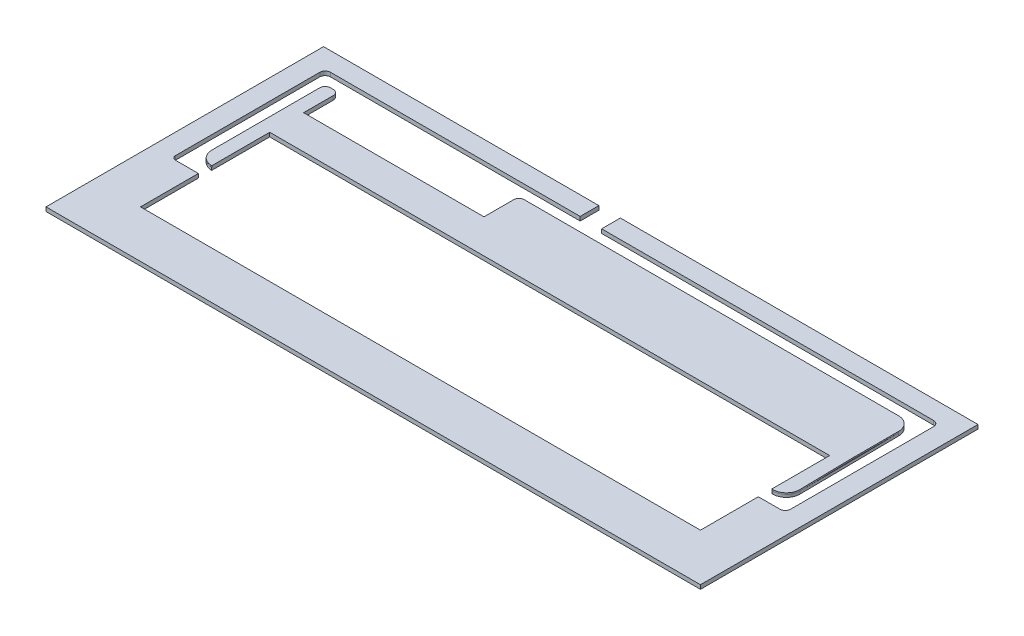
SolidWorks part; units mm, degrees
other "Marca1"
sketch "Croquis6" plane through (483.1, 12, 3.1) normal (0.4175, 0.3737, 0.8283) x (0.8528, 0.1536, -0.4991)
material "Balsa"
ref_plane "Alzado" through (0, 0, 0) normal (0, 0, 1) x (1, 0, 0)
ref_plane "Planta" through (0, 0, 0) normal (0, 1, 0) x (1, 0, 0)
ref_plane "Vista lateral" through (0, 0, 0) normal (1, 0, 0) x (0, 0, -1)
sketch "Croquis1" plane through (0, 0, 0) normal (0, 1, 0) x (1, 0, 0)
  line L0 (0, 0) -> (-3.1, 0) construction
  line L1 (0, 0) -> (480, 0)
  line L2 (0, 0) -> (0, 200)
  line L3 (0, 200) -> (480, 200)
  line L4 (480, 0) -> (480, 200)
  line L5 (0, 0) -> (0, -3.1) construction
  line L6 (-3.1, 0) -> (-3.1, -3.1) construction
  line L7 (-3.1, -3.1) -> (0, -3.1) construction
  line L8 (480, 200) -> (480, 203.1) construction
  line L9 (480, 203.1) -> (483.1, 203.1) construction
  line L11 (-3.1, -3.1) -> (483.1, -3.1)
  line L12 (-3.1, -3.1) -> (-3.1, 203.1)
  line L13 (-3.1, 203.1) -> (483.1, 203.1)
  line L14 (483.1, -3.1) -> (483.1, 203.1)
extrude "Saliente-Extruir1" add sketch "Croquis1" along normal blind 12 contours L1 L4 L3 L2 | L11 L14 L13 L12 L4 L1 L2 L3
sketch "Croquis2" plane through (0, 12, 0) normal (0, 1, 0) x (1, 0, 0)
  line L0 (21.9636, 184.1902) -> (21.9636, 179.1902) construction
  line L1 (17, 184.1902) -> (17, 189.1902) construction
  line L2 (17, 189.1902) -> (16, 189.1902)
  line L3 (28, 184.1902) -> (58, 184.1902) construction
  line L4 (32, 128) -> (448, 128)
  line L6 (32, 32) -> (448, 32)
  line L8 (32, 128) -> (448, 32) construction
  line L9 (32, 32) -> (448, 128) construction
  line L10 (32, 80) -> (17, 80) construction
  line L15 (17, 184.1902) -> (12, 184.1902) construction
  line L16 (28, 184.1902) -> (17, 184.1902) construction
  line L17 (17, 184.1902) -> (17, 80) construction
  line L18 (17, 184.1902) -> (17, 149.1902) construction
  line L19 (12, 185.1902) -> (12, 184.1902)
  line L20 (12, 146.1902) -> (12, 184.1902)
  line L21 (463, 189.1902) -> (464, 189.1902)
  line L22 (17, 80) -> (12, 80) construction
  line L23 (17, 80) -> (17, 75) construction
  line L24 (12, 184.1902) -> (12, 80)
  line L25 (12, 80) -> (12, 78)
  line L26 (15, 75) -> (17, 75)
  line L27 (17, 75) -> (32, 75)
  line L28 (17, 80) -> (21.9636, 80) construction
  line L29 (468, 185.1902) -> (468, 79)
  line L30 (31.9636, 85) -> (32, 85)
  line L31 (463, 189.1902) -> (448, 189.1902)
  line L32 (21.9636, 95) -> (21.9636, 175.1902)
  line L33 (25.9636, 179.1902) -> (28, 179.1902)
  line L34 (58, 184.1902) -> (448, 184.1902) construction
  line L35 (448, 80) -> (463, 80) construction
  line L36 (463, 80) -> (463, 184.1902) construction
  line L37 (463, 184.1902) -> (448, 184.1902) construction
  line L38 (459, 75) -> (459, 85) construction
  line L39 (448.8054, 85) -> (448, 85)
  line L40 (459, 75) -> (448, 75)
  line L41 (458.8036, 95.1927) -> (458.0364, 135)
  line L42 (32, 179.1902) -> (32, 189.1902) construction
  line L43 (448.0364, 125) -> (448, 125)
  line L44 (32, 189.1902) -> (17, 189.1902)
  line L45 (458.0364, 135) -> (458.0364, 169.1902)
  line L46 (464, 75) -> (459, 75)
  line L47 (166, 189.1902) -> (448, 189.1902)
  line L48 (32, 189.1902) -> (166, 189.1902)
  line L50 (32, 153.1902) -> (166, 153.1902)
  line L52 (448.0364, 179.1902) -> (170, 179.1902)
  line L53 (166, 175.1902) -> (166, 153.1902)
  line L54 (32, 175.1902) -> (32, 153.1902)
  line L55 (32, 128) -> (32, 85)
  line L56 (32, 75) -> (32, 32)
  line L57 (32, 85) -> (32, 75)
  line L58 (448, 128) -> (448, 85)
  line L59 (448, 32) -> (448, 75)
  line L60 (448, 85) -> (448, 75)
  line L61 (201.4487, 189.1902) -> (201.4487, 203.1)
  line L62 (-3.1, 203.1) -> (483.1, 203.1) construction
  line L63 (201.4487, 203.1) -> (217.4247, 203.1)
  line L64 (217.4247, 203.1) -> (217.4247, 189.1902)
  arc A0 (458.8036, 95.1927) -> (448.8054, 85) centre (448.8054, 95) cw
  arc A1 (458.0364, 169.1902) -> (448.0364, 179.1902) centre (448.0364, 169.1902) ccw
  arc A2 (21.9636, 95) -> (31.9636, 85) centre (31.9636, 95) ccw
  arc A3 (16, 189.1902) -> (12, 185.1902) centre (16, 185.1902) ccw
  arc A4 (464, 189.1902) -> (468, 185.1902) centre (464, 185.1902) cw
  arc A5 (468, 79) -> (464, 75) centre (464, 79) cw
  arc A6 (170, 179.1902) -> (166, 175.1902) centre (170, 175.1902) ccw
  arc A7 (12, 78) -> (15, 75) centre (15, 78) ccw
  arc A8 (21.9636, 175.1902) -> (25.9636, 179.1902) centre (25.9636, 175.1902) cw
  arc A9 (28, 179.1902) -> (32, 175.1902) centre (28, 175.1902) cw
  point P6 (240, 80)
  dimension "D1" = 10
  dimension "D2" = 4
  dimension "D3" = 4
sketch "Croquis3" plane through (0, 12, 0) normal (0, 1, 0) x (1, 0, 0)
  line L1 (0, 0) -> (480, 0)
  line L2 (0, 0) -> (0, 200)
  line L3 (0, 200) -> (480, 200)
  line L4 (480, 0) -> (480, 200)
  line L5 (-3.1, -3.1) -> (483.1, -3.1)
  line L6 (-3.1, -3.1) -> (-3.1, 203.1)
  line L7 (-3.1, 203.1) -> (483.1, 203.1)
  line L8 (483.1, -3.1) -> (483.1, 203.1)
extrude "Cortar-Extruir1" cut sketch "Croquis3" against normal blind 5
extrude "Cortar-Extruir3" cut sketch "Croquis2" against normal blind 8
sketch "Croquis4" plane through (0, 12, 0) normal (0, 1, 0) x (1, 0, 0)
  line L0 (32, 128) -> (32, 134)
  line L1 (32, 134) -> (52, 134)
  line L2 (52, 134) -> (52, 128)
  line L3 (32, 128) -> (448, 128) construction
  line L4 (52, 128) -> (32, 128)
  line L5 (240, 32) -> (240, 128) construction
  line L6 (32, 32) -> (448, 32) construction
  line L7 (32, 128) -> (448, 128) construction
  line L8 (240, 80) -> (282.8706, 80) construction
  line L9 (428, 134) -> (428, 128)
  line L10 (448, 128) -> (448, 134)
  line L11 (428, 128) -> (448, 128)
  line L12 (448, 134) -> (428, 134)
  line L13 (448, 32) -> (448, 26)
  line L14 (428, 32) -> (448, 32)
  line L15 (448, 26) -> (428, 26)
  line L16 (428, 26) -> (428, 32)
  line L17 (52, 26) -> (52, 32)
  line L18 (52, 32) -> (32, 32)
  line L19 (32, 26) -> (52, 26)
  line L20 (32, 32) -> (32, 26)
  line L21 (32, 75) -> (32, 69)
  line L22 (32, 75) -> (32, 32) construction
  line L23 (12, 80) -> (6, 80) construction
  line L24 (12, 185.1902) -> (12, 78) construction
  line L25 (32, 69) -> (6, 69)
  line L26 (16, 189.1902) -> (16, 195.1902) construction
  line L27 (6, 69) -> (6, 80)
  line L28 (6, 80) -> (6, 195.1902)
  line L29 (6, 195.1902) -> (16, 195.1902)
  line L30 (32, 189.1902) -> (32, 195.1902)
  line L31 (16, 189.1902) -> (201.4487, 189.1902) construction
  line L32 (32, 195.1902) -> (16, 195.1902)
  line L33 (16, 189.1902) -> (32, 189.1902)
  line L34 (12, 185.1902) -> (12, 80)
  line L35 (32, 75) -> (15, 75)
  line L36 (12, 80) -> (12, 78)
  line L37 (31.9636, 85) -> (32, 128)
  line L38 (32, 175.1902) -> (32, 134)
  line L39 (25.9636, 179.1902) -> (28, 179.1902)
  line L40 (21.9636, 175.1902) -> (21.9636, 95)
  line L41 (99, 153.1902) -> (99, 189.1902) construction
  line L42 (32, 153.1902) -> (52, 153.1902)
  line L43 (32, 153.1902) -> (32, 147.1902)
  line L44 (32, 147.1902) -> (52, 147.1902)
  line L45 (52, 153.1902) -> (52, 147.1902)
  line L46 (32, 153.1902) -> (166, 153.1902) construction
  line L47 (99, 171.1902) -> (116.5825, 171.1902) construction
  line L48 (52, 189.1902) -> (52, 195.1902)
  line L49 (32, 195.1902) -> (52, 195.1902)
  line L50 (32, 189.1902) -> (52, 189.1902)
  line L51 (146, 189.1902) -> (146, 195.1902)
  line L52 (166, 189.1902) -> (146, 189.1902)
  line L53 (166, 195.1902) -> (146, 195.1902)
  line L54 (166, 189.1902) -> (166, 195.1902)
  line L55 (166, 153.1902) -> (146, 153.1902)
  line L56 (166, 153.1902) -> (166, 147.1902)
  line L57 (146, 153.1902) -> (146, 147.1902)
  line L58 (166, 147.1902) -> (146, 147.1902)
  line L59 (468, 185.1902) -> (474, 185.1902) construction
  line L60 (464, 189.1902) -> (464, 195.1902) construction
  line L61 (464, 195.1902) -> (474, 195.1902) construction
  line L62 (166, 147.1902) -> (474, 147.1902) construction
  line L63 (448, 75) -> (448, 69) construction
  line L64 (166, 195.1902) -> (474, 195.1902)
  line L65 (166, 195.1902) -> (166, 147.1902)
  line L66 (166, 147.1902) -> (474, 147.1902)
  line L67 (474, 195.1902) -> (474, 147.1902)
  line L68 (448, 75) -> (448, 32) construction
  line L70 (474, 147.1902) -> (448, 147.1902)
  line L71 (474, 147.1902) -> (474, 69)
  line L72 (474, 69) -> (448, 69)
  line L73 (448, 147.1902) -> (448, 69)
  arc A0 (16, 189.1902) -> (12, 185.1902) centre (16, 185.1902) ccw
  arc A1 (12, 78) -> (15, 75) centre (15, 78) ccw
  arc A2 (21.9636, 95) -> (31.9636, 85) centre (31.9636, 95) ccw construction
  arc A3 (28, 179.1902) -> (32, 175.1902) centre (28, 175.1902) cw
  arc A4 (21.9636, 175.1902) -> (25.9636, 179.1902) centre (25.9636, 175.1902) cw
  arc A5 (21.9636, 95) -> (31.9636, 85) centre (31.9636, 95) ccw
  line M14 (32, 128) -> (448, 128)
  line M15 (448, 128) -> (448, 85)
  line M16 (448, 85) -> (448.8054, 85)
  arc M17 (448.8054, 85) -> (458.8036, 95.1927) centre (448.8054, 95) ccw
  line M18 (458.8036, 95.1927) -> (458.0364, 135)
  line M19 (458.0364, 135) -> (458.0364, 169.1902)
  arc M20 (458.0364, 169.1902) -> (448.0364, 179.1902) centre (448.0364, 169.1902) ccw
  line M21 (448.0364, 179.1902) -> (170, 179.1902)
  arc M22 (170, 179.1902) -> (166, 175.1902) centre (170, 175.1902) ccw
  line M23 (166, 175.1902) -> (166, 153.1902)
  line M24 (166, 153.1902) -> (32, 153.1902)
  line M25 (32, 153.1902) -> (32, 175.1902)
  arc M26 (32, 175.1902) -> (28, 179.1902) centre (28, 175.1902) ccw
  line M27 (28, 179.1902) -> (25.9636, 179.1902)
  arc M28 (25.9636, 179.1902) -> (21.9636, 175.1902) centre (25.9636, 175.1902) ccw
  line M29 (21.9636, 175.1902) -> (21.9636, 95)
  arc M30 (21.9636, 95) -> (31.9636, 85) centre (31.9636, 95) ccw
extrude "Cortar-Extruir4" cut sketch "Croquis4" against normal blind 3 contours L38 L37 L0 M25 M26 M27 M28 M29 M30 | L2 L1 L0 M14 | L45 L38 L44 M24 | A1 L36 L34 A0 L33 L30 L32 L29 L28 L27 L25 L21 L35 | L30 L50 L48 L49 | L18 L20 L19 L17 | L52 L54 L53 L51 | L58 L56 L57 M24 | L56 L66 M19 M20 M21 M22 M23 | L67 L64 L54 L65 L66 M22 M21 M20 M19 | L73 L72 L71 L66 M16 M19 M18 M17 | L10 L12 L9 M14 | L16 L15 L13 L14 | L66 L73 L10 M15 M16 M17 M18 M19
sketch "Croquis5" plane through (0, 4, 0) normal (0, 1, 0) x (1, 0, 0)
  line L0 (32.046, 84.9265) -> (32, 75)
  line L2 (32, 75) -> (15, 75)
  line L3 (25.9636, 179.1902) -> (28, 179.1902)
  line L4 (21.9636, 175.1902) -> (21.9636, 95)
  line L5 (32, 175.1902) -> (32, 153.1902)
  line L6 (32, 153.1902) -> (166, 153.1902)
  line L7 (166, 153.1902) -> (166, 175.1902)
  line L8 (170, 179.1902) -> (448.0364, 179.1902)
  line L9 (458.0364, 169.1902) -> (458.8036, 95.1927)
  line L10 (448.8054, 85) -> (448, 85)
  line L11 (448, 85) -> (448, 75)
  line L12 (448, 75) -> (464, 75)
  line L13 (468, 79) -> (468, 185.1902)
  line L14 (468, 185.1902) -> (468, 79) construction
  line L15 (464, 189.1902) -> (217.4247, 189.1902)
  line L16 (217.4247, 189.1902) -> (217.4247, 203.1)
  line L17 (217.4247, 203.1) -> (201.4487, 203.1)
  line L18 (201.4487, 203.1) -> (201.4487, 189.1902)
  line L19 (201.4487, 189.1902) -> (16, 189.1902)
  line L20 (12, 185.1902) -> (12, 78)
  arc A1 (12, 78) -> (15, 75) centre (15, 78) ccw
  arc A2 (25.9636, 179.1902) -> (21.9636, 175.1902) centre (25.9636, 175.1902) ccw
  arc A3 (21.9636, 95) -> (32.046, 84.9265) centre (32.0371, 95) ccw
  arc A4 (28, 179.1902) -> (32, 175.1902) centre (28, 175.1902) cw
  arc A5 (166, 175.1902) -> (170, 179.1902) centre (170, 175.1902) cw
  arc A6 (448.0364, 179.1902) -> (458.0364, 169.1902) centre (448.0364, 169.1902) cw
  arc A7 (448.8054, 85) -> (458.8036, 95.1927) centre (448.7156, 95.0881) ccw
  arc A8 (468, 79) -> (464, 75) centre (464, 79) cw
  arc A9 (468, 185.1902) -> (464, 189.1902) centre (464, 185.1902) ccw construction
  arc A10 (464, 189.1902) -> (468, 185.1902) centre (464, 185.1902) cw
  arc A11 (16, 189.1902) -> (12, 185.1902) centre (16, 185.1902) ccw
extrude "Cortar-Extruir5" cut sketch "Croquis5" against normal blind 2
sketch "Croquis7" plane through (0, 2, 0) normal (0, 1, 0) x (1, 0, 0)
  line L1 (-211.6054, 341.1803) -> (510.3417, 341.1803)
  line L2 (-211.6054, 341.1803) -> (-211.6054, -18.2396)
  line L3 (-211.6054, -18.2396) -> (510.3417, -18.2396)
  line L4 (510.3417, 341.1803) -> (510.3417, -18.2396)
  line L5 (-211.6054, 341.1803) -> (510.3417, -18.2396) construction
  line L6 (-211.6054, -18.2396) -> (510.3417, 341.1803) construction
  point P0 (149.3682, 161.4704)
extrude "Cortar-Extruir6" cut sketch "Croquis7" against normal blind 10
sketch "Croquis8" plane through (0, 4, 0) normal (0, 1, 0) x (1, 0, 0)
  line L1 (32, 128) -> (448, 128)
  line L2 (32, 128) -> (32, 32)
  line L3 (32, 32) -> (448, 32)
  line L4 (448, 128) -> (448, 32)
extrude "Cortar-Extruir7" cut sketch "Croquis8" against normal blind 10
sketch "Croquis9" plane through (0, 9, 0) normal (0, 1, 0) x (1, 0, 0)
  line L1 (512.9567, 229.5955) -> (-18.948, 229.5955)
  line L2 (512.9567, 229.5955) -> (512.9567, -16.7579)
  line L3 (512.9567, -16.7579) -> (-18.948, -16.7579)
  line L4 (-18.948, 229.5955) -> (-18.948, -16.7579)
  point P4 (425.7612, 15.2567)
  point P5 (512.9567, 229.5955)
sketch "Croquis10" plane through (0, 7, 0) normal (0, 1, 0) x (1, 0, 0)
  line L1 (-18.948, 229.5955) -> (512.9567, 229.5955)
  line L2 (-18.948, 229.5955) -> (-18.948, -16.7579)
  line L3 (-18.948, -16.7579) -> (512.9567, -16.7579)
  line L4 (512.9567, 229.5955) -> (512.9567, -16.7579)
ref_plane "Plano1" through (0, 5, 0) normal (0, -1, 0) x (-1, 0, 0)
sketch "Croquis11" plane through (0, 5, 0) normal (0, -1, 0) x (-1, 0, 0)
  line L1 (-512.9567, 229.5955) -> (18.948, 229.5955)
  line L2 (-512.9567, 229.5955) -> (-512.9567, -16.7579)
  line L3 (-512.9567, -16.7579) -> (18.948, -16.7579)
  line L4 (18.948, 229.5955) -> (18.948, -16.7579)
extrude "Cortar-Extruir9" cut sketch "Croquis9" along normal blind 10
extrude "Cortar-Extruir10" cut sketch "Croquis10" along normal blind 10 contours L1 L4 L3 L2
extrude "Cortar-Extruir11" cut sketch "Croquis11" against normal blind 10
